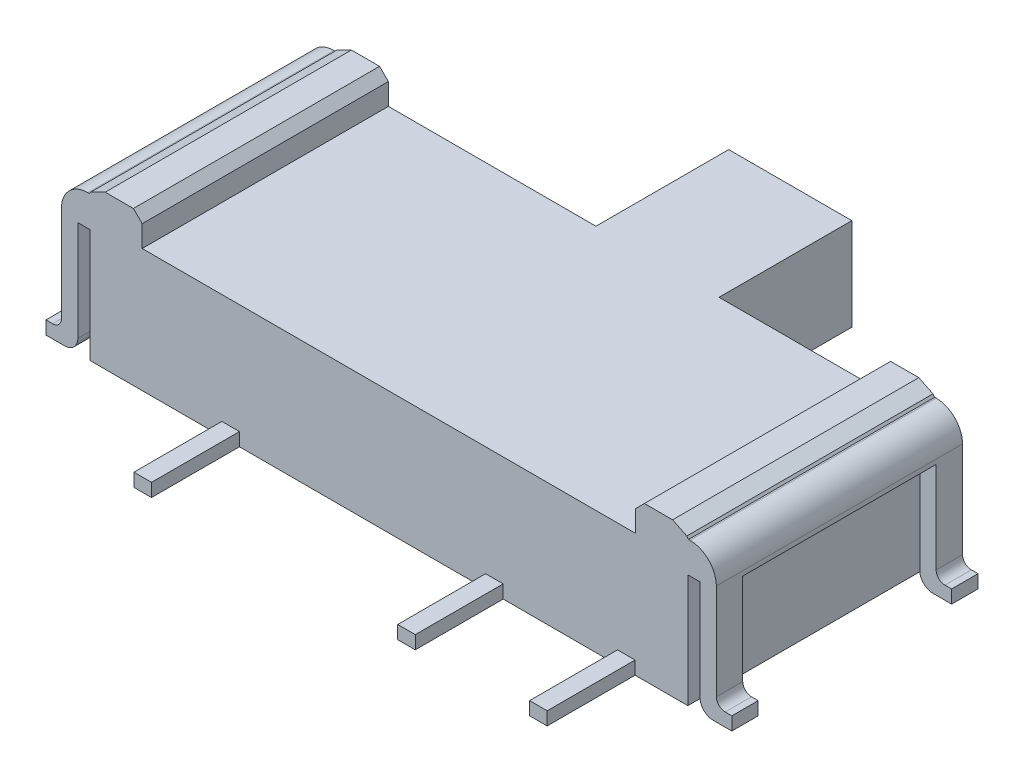
SolidWorks part; units mm, degrees
ref_plane "Front Plane" through (0, 0, 0) normal (0, 0, 1) x (1, 0, 0)
ref_plane "Top Plane" through (0, 0, 0) normal (0, 1, 0) x (1, 0, 0)
ref_plane "Right Plane" through (0, 0, 0) normal (1, 0, 0) x (0, 0, -1)
sketch "Sketch1" plane through (0, 0, 0) normal (0, 1, 0) x (1, 0, 0)
  line L1 (-3.4, 1.4) -> (3.4, 1.4)
  line L2 (-3.4, 1.4) -> (-3.4, -1.4)
  line L3 (-3.4, -1.4) -> (3.4, -1.4)
  line L4 (3.4, 1.4) -> (3.4, -1.4)
  line L5 (-3.4, 1.4) -> (3.4, -1.4) construction
  line L6 (-3.4, -1.4) -> (3.4, 1.4) construction
  point P0 (0, 0)
  dimension "D1" = 6.8
  dimension "D2" = 2.8
extrude "Boss-Extrude1" add sketch "Sketch1" along normal blind 1.4
sketch "Sketch3" plane through (0, 0, 1.4) normal (0, 0, 1) x (1, 0, 0)
  line L0 (0, 0) -> (0, 2.7608) construction
  line L1 (-3.9, 0) -> (-3.6878, 0)
  line L2 (-3.5378, 0.15) -> (-3.5378, 1.4455)
  line L3 (-3.5378, 1.4455) -> (-2.9329, 1.4455)
  line L4 (-2.9329, 1.4455) -> (-2.9329, 1.6411)
  line L5 (-2.9329, 1.6411) -> (-3.4242, 1.6411)
  line L6 (-3.7242, 1.3411) -> (-3.7242, 0.25)
  line L7 (-3.8242, 0.15) -> (-3.9, 0.15)
  line L8 (-3.9, 0.15) -> (-3.9, 0)
  line L9 (3.8242, 0.15) -> (3.9, 0.15)
  line L10 (3.7242, 1.3411) -> (3.7242, 0.25)
  line L11 (2.9329, 1.6411) -> (3.4242, 1.6411)
  line L12 (2.9329, 1.4455) -> (2.9329, 1.6411)
  line L13 (3.5378, 1.4455) -> (2.9329, 1.4455)
  line L14 (3.5378, 0.15) -> (3.5378, 1.4455)
  line L15 (3.9, 0) -> (3.6878, 0)
  line L16 (3.9, 0.15) -> (3.9, 0)
  arc A0 (-3.5378, 0.15) -> (-3.6878, 0) centre (-3.6878, 0.15) cw
  arc A1 (-3.7242, 0.25) -> (-3.8242, 0.15) centre (-3.8242, 0.25) cw
  arc A2 (-3.4242, 1.6411) -> (-3.7242, 1.3411) centre (-3.4242, 1.3411) ccw
  arc A3 (3.7242, 0.25) -> (3.8242, 0.15) centre (3.8242, 0.25) ccw
  arc A4 (3.4242, 1.6411) -> (3.7242, 1.3411) centre (3.4242, 1.3411) cw
  arc A5 (3.5378, 0.15) -> (3.6878, 0) centre (3.6878, 0.15) ccw
  dimension "D1" = 0.15
  dimension "D2" = 0.1
  dimension "D3" = 0.3
  dimension "D4" = 7.8
  dimension "D5" = 0.15
extrude "Boss-Extrude2" add sketch "Sketch3" against normal up to surface (2.8 mm away) separate body up to face at (0, 0.7, -1.4)
sketch "Sketch4" plane through (0, 0, 1.4) normal (0, 0, 1) x (1, 0, 0)
  line L0 (-2.806, 1.4) -> (-2.806, 1.6445)
  line L1 (-3.4, 1.4) -> (3.4, 1.4) construction
  line L2 (-2.906, 1.7445) -> (-3.2267, 1.7445)
  line L3 (-3.3883, 1.6657) -> (-3.6212, 1.3677)
  line L4 (-3.5828, 1.2889) -> (-2.806, 1.2889)
  line L5 (-2.806, 1.2889) -> (-2.806, 1.4)
  line L6 (-3.2267, 1.7445) -> (-3.3883, 1.6657)
  line L7 (-3.6212, 1.3677) -> (-3.5828, 1.2889)
  line L8 (-2.806, 1.6445) -> (-2.906, 1.7445)
  line L9 (0, 0) -> (0, 2.5734) construction
  line L10 (-3.4, 0) -> (3.4, 0) construction
  line L11 (3.5828, 1.2889) -> (2.806, 1.2889)
  line L12 (3.6212, 1.3677) -> (3.5828, 1.2889)
  line L13 (3.3883, 1.6657) -> (3.6212, 1.3677)
  line L14 (3.2267, 1.7445) -> (3.3883, 1.6657)
  line L15 (2.906, 1.7445) -> (3.2267, 1.7445)
  line L16 (2.806, 1.6445) -> (2.906, 1.7445)
  line L17 (2.806, 1.4) -> (2.806, 1.6445)
  line L18 (2.806, 1.2889) -> (2.806, 1.4)
  point P1 (-2.806, 1.7445)
  point P4 (-3.3267, 1.7445)
  point P5 (-3.6828, 1.2889)
extrude "Boss-Extrude3" add sketch "Sketch4" against normal up to surface (2.8 mm away) up to face at (0, 0.7, -1.4)
sketch "Sketch5" plane through (0, 1.4, 0) normal (0, 1, 0) x (1, 0, 0)
  line L0 (-3.9, 0) -> (3.9, 0) construction
  line L1 (-3.9, 1.4) -> (-3.9, -1.4) construction
  line L2 (3.9, 1.4) -> (3.9, -1.4) construction
ref_plane "Plane1" through (0, 0, 0) normal (0, 0, 1) x (1, 0, 0)
sketch "Sketch6" plane through (0, 0, 0) normal (0, 0, 1) x (1, 0, 0)
  line L0 (-3.5378, 1.2889) -> (-3.7242, 1.2889)
  line L1 (3.5378, 1.2889) -> (3.7242, 1.2889)
  line L8 (3.9, 0.15) -> (3.8242, 0.15)
  line L9 (3.9, 0) -> (3.9, 0.15)
  line L10 (3.6878, 0) -> (3.9, 0)
  line L11 (3.5378, 1.4455) -> (3.5378, 0.15)
  line L12 (2.9329, 1.4455) -> (3.5378, 1.4455)
  line L13 (2.9329, 1.6411) -> (2.9329, 1.4455)
  line L14 (3.4242, 1.6411) -> (2.9329, 1.6411)
  line L15 (3.7242, 0.25) -> (3.7242, 1.3411)
  line L16 (3.9, 0.15) -> (3.8242, 0.15)
  line L17 (3.9, 0) -> (3.9, 0.15)
  line L18 (3.6878, 0) -> (3.9, 0)
  line L19 (3.5378, 1.2889) -> (3.5378, 0.15)
  line L23 (3.7242, 0.25) -> (3.7242, 1.2889)
  line L24 (-2.9329, 1.6411) -> (-3.4242, 1.6411)
  line L25 (-2.9329, 1.4455) -> (-2.9329, 1.6411)
  line L26 (-3.5378, 1.4455) -> (-2.9329, 1.4455)
  line L27 (-3.5378, 0.15) -> (-3.5378, 1.4455)
  line L28 (-3.9, 0) -> (-3.6878, 0)
  line L29 (-3.9, 0.15) -> (-3.9, 0)
  line L30 (-3.8242, 0.15) -> (-3.9, 0.15)
  line L31 (-3.7242, 1.3411) -> (-3.7242, 0.25)
  line L35 (-3.5378, 0.15) -> (-3.5378, 1.2889)
  line L36 (-3.9, 0) -> (-3.6878, 0)
  line L37 (-3.9, 0.15) -> (-3.9, 0)
  line L38 (-3.8242, 0.15) -> (-3.9, 0.15)
  line L39 (-3.7242, 1.2889) -> (-3.7242, 0.25)
  arc A3 (3.5378, 0.15) -> (3.6878, 0) centre (3.6878, 0.15) ccw
  arc A4 (3.7242, 1.3411) -> (3.4242, 1.6411) centre (3.4242, 1.3411) ccw
  arc A5 (3.7242, 0.25) -> (3.8242, 0.15) centre (3.8242, 0.25) ccw
  arc A6 (3.5378, 0.15) -> (3.6878, 0) centre (3.6878, 0.15) ccw
  arc A8 (3.7242, 0.25) -> (3.8242, 0.15) centre (3.8242, 0.25) ccw
  arc A9 (-3.4242, 1.6411) -> (-3.7242, 1.3411) centre (-3.4242, 1.3411) ccw
  arc A10 (-3.6878, 0) -> (-3.5378, 0.15) centre (-3.6878, 0.15) ccw
  arc A11 (-3.8242, 0.15) -> (-3.7242, 0.25) centre (-3.8242, 0.25) ccw
  arc A13 (-3.6878, 0) -> (-3.5378, 0.15) centre (-3.6878, 0.15) ccw
  arc A14 (-3.8242, 0.15) -> (-3.7242, 0.25) centre (-3.8242, 0.25) ccw
  dimension "D1" = 0
  dimension "D2" = 0
extrude "Cut-Extrude1" cut sketch "Sketch6" against normal mid plane 2.2
sketch "Sketch8" plane through (0, 0, 0) normal (0, -1, 0) x (1, 0, 0)
  line L0 (-3.4, 1.4) -> (3.4, 1.4) construction
  line L1 (-1.9, 1.4) -> (-1.7, 1.4)
  line L2 (-1.9, 1.4) -> (-1.9, 2.4)
  line L3 (-1.9, 2.4) -> (-1.7, 2.4)
  line L4 (-1.7, 1.4) -> (-1.7, 2.4)
  line L5 (3.4, -1.4) -> (3.4, 1.4) construction
  line L6 (1.1, 1.4) -> (1.3, 1.4)
  line L7 (1.1, 1.4) -> (1.1, 2.4)
  line L8 (1.1, 2.4) -> (1.3, 2.4)
  line L9 (1.3, 1.4) -> (1.3, 2.4)
  line L10 (2.6, 1.4) -> (2.8, 1.4)
  line L11 (2.6, 1.4) -> (2.6, 2.4)
  line L12 (2.6, 2.4) -> (2.8, 2.4)
  line L13 (2.8, 1.4) -> (2.8, 2.4)
  point P14 (2.7, 2.4)
  point P15 (1.2, 2.4)
  point P18 (-1.8, 2.4)
  dimension "D1" = 1
  dimension "D2" = 0.2
  dimension "D3" = 1.5
  dimension "D4" = 0.6
  dimension "D5" = 3
extrude "Boss-Extrude4" add sketch "Sketch8" against normal blind 0.15
sketch "Sketch9" plane through (0, 0, -1.4) normal (0, 0, -1) x (-1, 0, 0)
  line L0 (-2.806, 1.4) -> (2.806, 1.4) construction
  line L1 (-0.9547, 1.4) -> (0.4453, 1.4)
  line L2 (-0.9547, 1.4) -> (-0.9547, 0.35)
  line L3 (-0.9547, 0.35) -> (0.4453, 0.35)
  line L4 (0.4453, 1.4) -> (0.4453, 0.35)
  dimension "D1" = 1.4
  dimension "D2" = 1.05
extrude "Boss-Extrude5" add sketch "Sketch9" along normal blind 1.51
